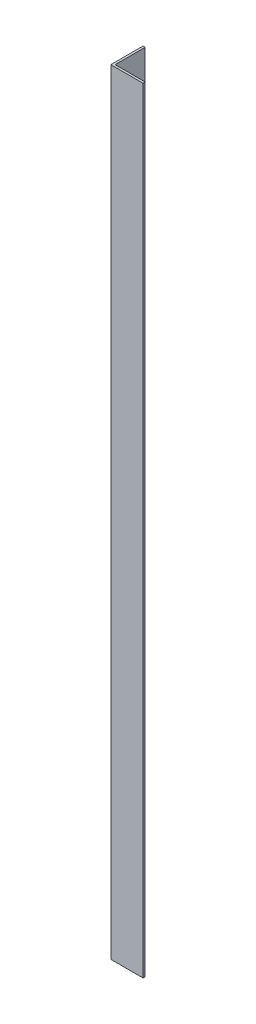
SolidWorks part; units mm, degrees
material "1060 Сплав"
ref_plane "Спереди" through (0, 0, 0) normal (0, 0, 1) x (1, 0, 0)
ref_plane "Сверху" through (0, 0, 0) normal (0, 1, 0) x (1, 0, 0)
ref_plane "Справа" through (0, 0, 0) normal (1, 0, 0) x (0, 0, -1)
sketch "Эскиз1" plane through (0, 0, 0) normal (0, 1, 0) x (1, 0, 0)
  line L0 (0, 0) -> (0, 15)
  line L1 (0, 15) -> (1, 15)
  line L2 (1, 15) -> (1, 1)
  line L3 (1, 1) -> (15, 1)
  line L4 (15, 1) -> (15, 0)
  line L5 (15, 0) -> (0, 0)
  dimension "D1" = 1
  dimension "D2" = 15
extrude "Бобышка-Вытянуть1" add sketch "Эскиз1" along normal blind 360
